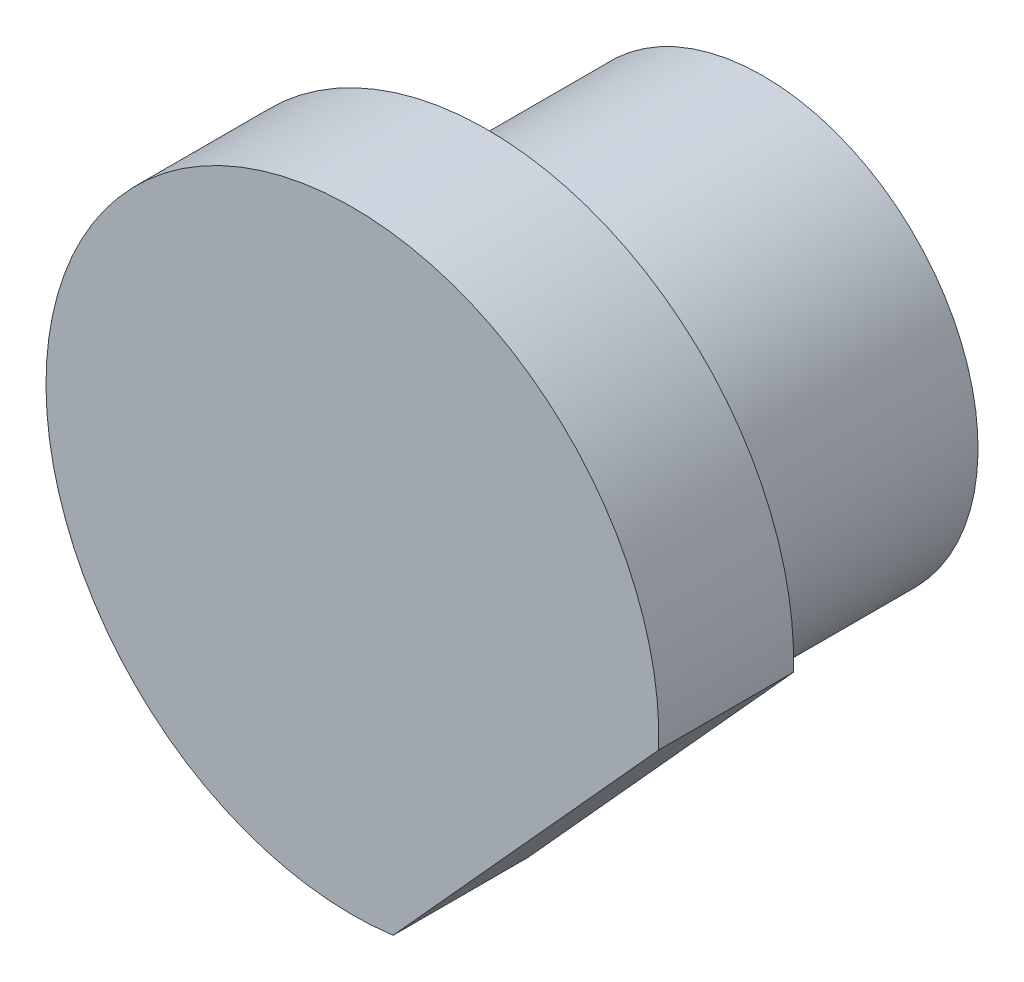
SolidWorks part; units mm, degrees
ref_plane "Спереди" through (0, 0, 0) normal (0, 0, 1) x (1, 0, 0)
ref_plane "Сверху" through (0, 0, 0) normal (0, 1, 0) x (1, 0, 0)
ref_plane "Справа" through (0, 0, 0) normal (1, 0, 0) x (0, 0, -1)
sketch "Эскиз2" plane through (0, 0, 0) normal (0, 1, 0) x (1, 0, 0)
  circle A0 centre (0, 0) radius 3.5013
extrude "Бобышка-Вытянуть1" add sketch "Эскиз2" along normal blind 4.4919
sketch "Эскиз3" plane through (0, 0, 0) normal (0, -1, 0) x (-1, 0, 0)
  line L0 (-0.6625, 4.9457) -> (-4.9869, 0.1707)
  arc A0 (-4.9869, 0.1707) -> (-0.6625, 4.9457) centre (0, 0) ccw
extrude "Бобышка-Вытянуть2" add sketch "Эскиз3" along normal blind 2.1934
move or copy body "Тело-Переместить/Копировать1" bodies to move or copy 104 copy no rotation origin (0, 1.1493, 0) rotation axis (-1, 0, 0) rotation angle 90
move or copy body "Тело-Переместить/Копировать2" bodies to move or copy 107 copy no translate (0, 0, -3.34)
